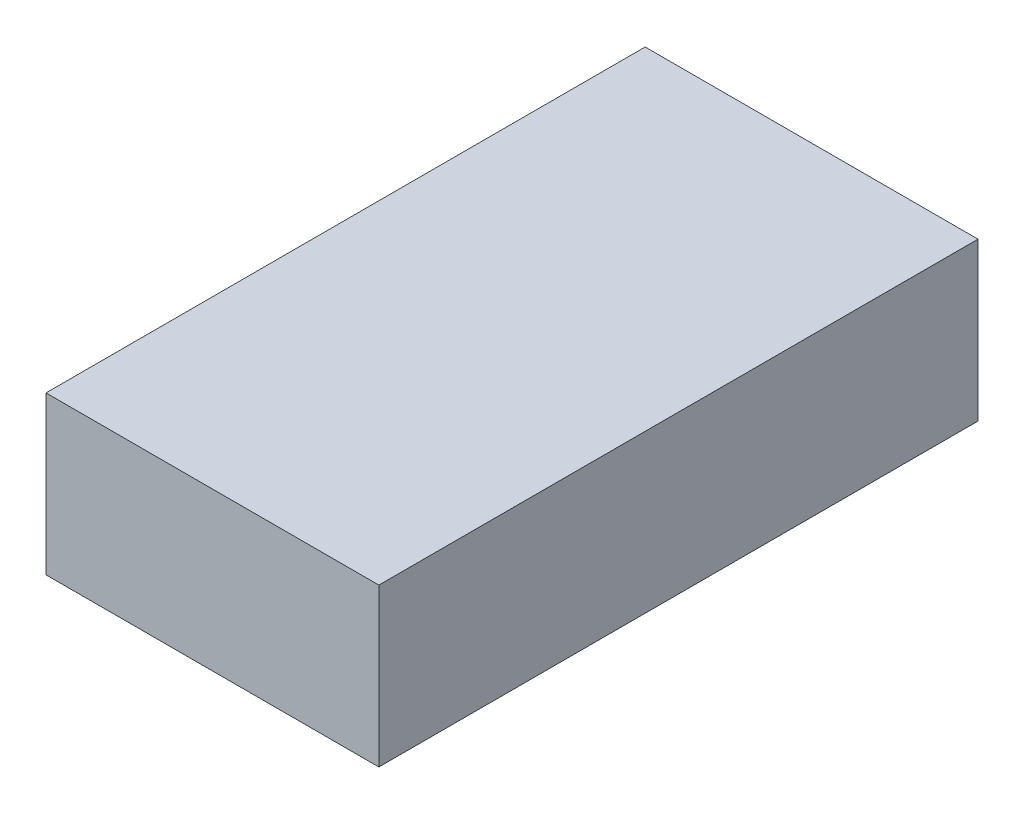
SolidWorks part; units mm, degrees
ref_plane "Front Plane" through (0, 0, 0) normal (0, 0, 1) x (1, 0, 0)
ref_plane "Top Plane" through (0, 0, 0) normal (0, 1, 0) x (1, 0, 0)
ref_plane "Right Plane" through (0, 0, 0) normal (1, 0, 0) x (0, 0, -1)
sketch "Sketch1" plane through (0, 0, 0) normal (0, 1, 0) x (1, 0, 0)
  line L1 (0, 0) -> (38.1, 0)
  line L2 (0, 0) -> (0, 68.58)
  line L3 (0, 68.58) -> (38.1, 68.58)
  line L4 (38.1, 0) -> (38.1, 68.58)
  dimension "D1" = 68.58
  dimension "D2" = 38.1
extrude "Boss-Extrude1" add sketch "Sketch1" along normal blind 18.034
